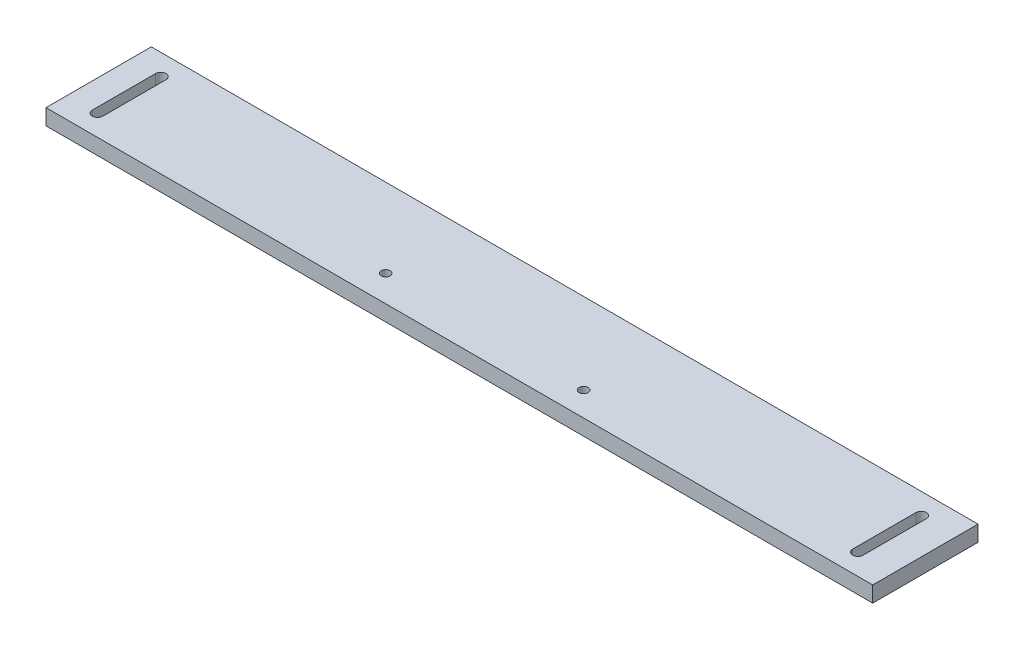
SolidWorks part; units mm, degrees
ref_plane "Alzado" through (0, 0, 0) normal (0, 0, 1) x (1, 0, 0)
ref_plane "Planta" through (0, 0, 0) normal (0, 1, 0) x (1, 0, 0)
ref_plane "Vista lateral" through (0, 0, 0) normal (1, 0, 0) x (0, 0, -1)
sketch "Croquis1" plane through (0, 0, 0) normal (0, 1, 0) x (1, 0, 0)
  line L1 (-38.5634, 7.6669) -> (746.4366, 7.6669)
  line L2 (-38.5634, 7.6669) -> (-38.5634, -92.3331)
  line L3 (-38.5634, -92.3331) -> (746.4366, -92.3331)
  line L4 (746.4366, 7.6669) -> (746.4366, -92.3331)
  dimension "D1" = 785
  dimension "10.2" = 100
extrude "Saliente-Extruir1" add sketch "Croquis1" against normal blind 15 contours L1 L4 L3 L2
sketch "Croquis5" plane through (0, 0, 0) normal (0, 1, 0) x (1, 0, 0)
  line L0 (-38.5634, -92.3331) -> (746.4366, -92.3331) construction
  line L1 (-38.5634, 7.6669) -> (-38.5634, -92.3331) construction
  circle A0 centre (258.9366, -67.3331) radius 4.25
  circle A1 centre (448.9261, -69.333) radius 4.25
  dimension "D1" = 8.5
  dimension "D4" = 8.5
  dimension "D2" = 25
  dimension "D3" = 297.5
  dimension "D5" = 190
extrude "Cortar-Extruir4" cut sketch "Croquis5" against normal through all
sketch "Croquis6" plane through (0, 0, 0) normal (0, 1, 0) x (1, 0, 0)
  line L1 (-38.5634, 7.6669) -> (746.4366, 7.6669) construction
  line L2 (-38.5634, 7.6669) -> (-38.5634, -92.3331) construction
  line L3 (-38.5634, -92.3331) -> (746.4366, -92.3331) construction
  line L4 (717.4366, -72.3331) -> (717.4366, -12.3331)
  line L5 (707.4366, -72.3331) -> (707.4366, -12.3331)
  line L6 (746.4366, 7.6669) -> (746.4366, -92.3331) construction
  line L7 (-4.5634, -12.3331) -> (-4.5634, -72.3331)
  line L8 (-14.5634, -12.3331) -> (-14.5634, -72.3331)
  arc A0 (707.4366, -72.3331) -> (717.4366, -72.3331) centre (712.4366, -72.3331) ccw
  arc A2 (717.4366, -12.3331) -> (707.4366, -12.3331) centre (712.4366, -12.3331) ccw
  arc A3 (-4.5634, -12.3331) -> (-14.5634, -12.3331) centre (-9.5634, -12.3331) ccw
  arc A4 (-14.5634, -72.3331) -> (-4.5634, -72.3331) centre (-9.5634, -72.3331) ccw
  dimension "D4" = 60
  dimension "D5" = 10
  dimension "D10" = 60
  dimension "D11" = 10
  dimension "D3" = 10
  dimension "D2" = 29
  dimension "D6" = 20
  dimension "D7" = 20
  dimension "D8" = 20
  dimension "D9" = 20
  dimension "D12" = 29
extrude "Cortar-Extruir5" cut sketch "Croquis6" against normal through all
